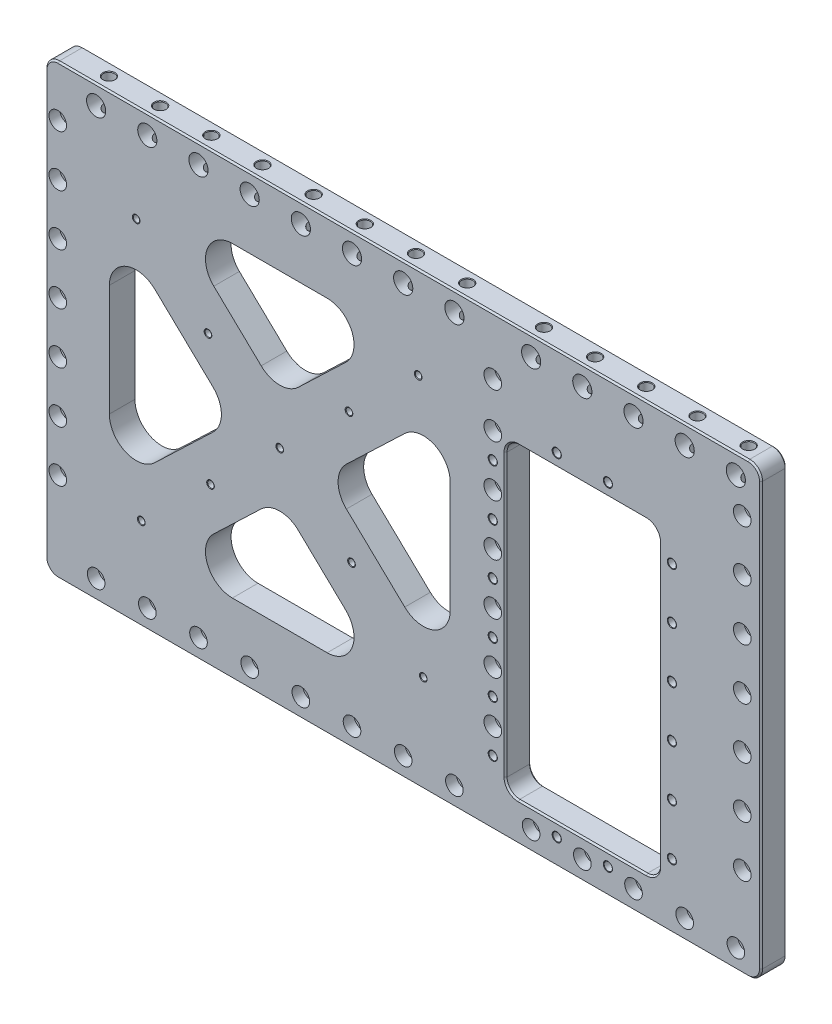
SolidWorks part; units mm, degrees
material "6061-T6 Al"
ref_plane "Front Plane" through (0, 0, 0) normal (0, 0, 1) x (1, 0, 0)
ref_plane "Top Plane" through (0, 0, 0) normal (0, 1, 0) x (1, 0, 0)
ref_plane "Right Plane" through (0, 0, 0) normal (1, 0, 0) x (0, 0, -1)
sketch "Sketch1" plane through (0, 0, 0) normal (0, 0, 1) x (1, 0, 0)
  line L0 (-355.219, -222.25) -> (355.219, 222.25) construction
  line L1 (-355.219, 222.25) -> (355.219, 222.25)
  line L2 (-355.219, 222.25) -> (-355.219, -222.25)
  line L3 (-355.219, -222.25) -> (355.219, -222.25)
  line L4 (355.219, 222.25) -> (355.219, -222.25)
  point P4 (0, 0)
  dimension "D1" = 710.438
  dimension "D2" = 444.5
extrude "Extrude1" add sketch "Sketch1" along normal mid plane 25.4
hole_wizard "CBORE for 3/8 Socket Head Cap Screw1" positions "Sketch3" profile "Sketch2" counterbore size "3/8" standard "Ansi Inch" end condition through all
sketch "Sketch3" plane through (0, 0, 12.7) normal (0, 0, 1) x (1, 0, 0)
  line L0 (-342.9, 19.05) -> (-355.219, 19.05) construction
  line L1 (-355.219, 222.25) -> (-355.219, -222.25) construction
  line L16 (-355.219, 222.25) -> (-355.219, -184.15) construction
  line L17 (336.55, 19.05) -> (-342.9, 19.05) construction
  point P0 (-342.9, 19.05)
  point P32 (336.55, 19.05)
  point P58 (-355.219, 19.05)
  dimension "D1" = 679.45
  dimension "D2" = 406.4
  dimension "D3" = 342.9
sketch "Sketch2" plane through (-342.9, 19.05, 12.7) normal (1, 0, 0) x (0, -1, 0)
  line L0 (0, 0) -> (0, 25.4)
  line L1 (5.1587, 24.614) -> (5.842, 25.4)
  line L2 (5.1587, 24.614) -> (5.1587, 10.668)
  line L3 (5.1587, 10.668) -> (8.7376, 10.668)
  line L4 (8.7376, 10.668) -> (8.7376, 0)
  line L5 (8.7376, 0) -> (0, 0)
  line L11 (0, -6.35) -> (0, 107.95) construction
  line L12 (5.842, 25.4) -> (0, 25.4)
  line L13 (-5.1587, 24.614) -> (-5.842, 25.4) construction
  dimension "Thru Hole Dia." = 10.3175
  dimension "Thru Hole Depth" = 25.4
  dimension "C'Bore Dia." = 17.4752
  dimension "C'Bore Depth" = 10.668
  dimension "Far C'Sink Dia." = 11.684
  dimension "Far C'Sink Angle" = 82
pattern_linear "LPattern1" count 4 spacing 50.8 along (0, -1, 0) count 4 spacing 50.8 along (0, 1, 0) of "CBORE for 3/8 Socket Head Cap Screw1"
sketch "Sketch9" plane through (0, 0, 12.7) normal (0, 0, 1) x (1, 0, 0)
  line L0 (-355.219, 222.25) -> (110.1219, -222.25) construction
  line L1 (-355.219, -222.25) -> (110.1219, 222.25) construction
  line L2 (-122.5485, 0) -> (-122.5485, 43.9073) construction
  line L3 (-122.5485, 0) -> (-168.5145, 0) construction
  line L4 (-8.9691, 152.4) -> (-122.5485, 43.9073)
  line L5 (-122.5485, 43.9073) -> (-236.128, 152.4)
  line L6 (-236.128, 152.4) -> (-8.9691, 152.4)
  line L7 (-291.719, 117.6866) -> (-168.5145, 0)
  line L8 (-168.5145, 0) -> (-291.719, -117.6866)
  line L9 (-291.719, -117.6866) -> (-291.719, 117.6866)
  line L10 (-122.5485, -43.9073) -> (-236.128, -152.4)
  line L11 (-236.128, -152.4) -> (-8.9691, -152.4)
  line L12 (-8.9691, -152.4) -> (-122.5485, -43.9073)
  line L13 (46.6219, 117.6866) -> (46.6219, -117.6866)
  line L14 (46.6219, -117.6866) -> (-76.5826, 0)
  line L15 (-76.5826, 0) -> (46.6219, 117.6866)
  line L16 (-122.5485, 0) -> (-76.5826, 0) construction
  line L17 (-122.5485, -43.9073) -> (-122.5485, 0) construction
  line L18 (355.219, 222.25) -> (-355.219, 222.25) construction
  line L20 (110.1219, -133.35) -> (110.1219, -222.25) construction
  line L21 (-355.219, 222.25) -> (-355.219, -222.25) construction
  dimension "D1" = 63.5
  dimension "D2" = 69.85
  dimension "D3" = 63.5
  dimension "D5" = 232.6705
extrude "Cut-Extrude2" cut sketch "Sketch9" against normal through all
fillet "Fillet2" radius 26.67 12 edges at (-236.128, 152.4, 0) (-8.9691, 152.4, 0) (-122.5485, 43.9073, 0) (-76.5826, 0, 0) (46.6219, 117.6866, 0) (46.6219, -117.6866, 0) (-8.9691, -152.4, 0) (-122.5485, -43.9073, 0) (-236.128, -152.4, 0) (-291.719, -117.6866, 0) (-168.5145, 0, 0) (-291.719, 117.6866, 0)
hole_wizard "CBORE for 3/8 Socket Head Cap Screw2" positions "Sketch5" profile "Sketch4" counterbore size "3/8" standard "Ansi Inch" end condition through all
sketch "Sketch5" plane through (0, 0, 12.7) normal (0, 0, 1) x (1, 0, 0)
  line L19 (355.219, 222.25) -> (-355.219, 222.25) construction
  point P74 (-152.4, -203.2)
  dimension "D1" = 425.45
  dimension "D2" = 152.4
sketch "Sketch4" plane through (-152.4, -203.2, 12.7) normal (1, 0, 0) x (0, -1, 0)
  line L0 (0, 0) -> (0, 25.4)
  line L1 (5.1587, 24.614) -> (5.842, 25.4)
  line L2 (5.1587, 24.614) -> (5.1587, 10.668)
  line L3 (5.1587, 10.668) -> (8.7376, 10.668)
  line L4 (8.7376, 10.668) -> (8.7376, 0)
  line L5 (8.7376, 0) -> (0, 0)
  line L11 (0, -6.35) -> (0, 107.95) construction
  line L12 (5.842, 25.4) -> (0, 25.4)
  line L13 (-5.1587, 24.614) -> (-5.842, 25.4) construction
  dimension "Thru Hole Dia." = 10.3175
  dimension "Thru Hole Depth" = 25.4
  dimension "C'Bore Dia." = 17.4752
  dimension "C'Bore Depth" = 10.668
  dimension "Far C'Sink Dia." = 11.684
  dimension "Far C'Sink Angle" = 82
hole_wizard "7/16 (0.4375) Diameter Hole1" positions "Sketch15" profile "Sketch14" hole size "7/16" standard "Ansi Inch"
sketch "Sketch15" plane through (0, 222.25, 0) normal (0, 1, 0) x (-1, 0, 0)
  line L10 (152.4, -12.7) -> (152.4, -11.914) construction
  point P0 (152.4, 0)
sketch "Sketch14" plane through (-152.4, 222.25, 0) normal (1, 0, 0) x (0, 0, 1)
  line L0 (0, 0) -> (0, 38.2635)
  line L1 (0, 38.2635) -> (5.5562, 34.925)
  line L2 (5.5562, 34.925) -> (5.5562, 0.6209)
  line L3 (5.5562, 0.6209) -> (6.096, 0)
  line L5 (6.096, 0) -> (0, 0)
  line L6 (-5.5562, 0.6209) -> (-6.096, 0) construction
  line L10 (0, 38.2635) -> (-5.5563, 34.925) construction
  line L11 (0, -6.35) -> (0, 107.95) construction
  dimension "Hole Dia." = 11.1125
  dimension "Hole Depth" = 34.925
  dimension "Near C'Sink Dia." = 12.192
  dimension "Near C'Sink Angle" = 82
  dimension "Drill Angle" = 118
hole_wizard "3/4 (0.75) Diameter Hole1" positions "Sketch13" profile "Sketch12" hole size "3/4" standard "Ansi Inch" end condition through all
sketch "Sketch13" plane through (0, 0, 12.7) normal (0, 0, 1) x (1, 0, 0)
  line L3 (-152.4, 187.325) -> (-152.4, 221.6291) construction
  line L4 (355.219, 222.25) -> (-355.219, 222.25) construction
  point P0 (-152.4, 203.2)
  dimension "D1" = 19.05
sketch "Sketch12" plane through (-152.4, 203.2, 12.7) normal (1, 0, 0) x (0, -1, 0)
  line L0 (0, 0) -> (0, 25.4)
  line L1 (0, 25.4) -> (9.525, 25.4)
  line L2 (9.525, 25.4) -> (9.525, 0)
  line L5 (9.525, 0) -> (0, 0)
  line L11 (0, -6.35) -> (0, 107.95) construction
  dimension "Thru Hole Dia." = 19.05
  dimension "Thru Hole Depth" = 25.4
pattern_linear "LPattern4" count 4 spacing 50.8 along (-1, 0, 0) count 5 spacing 50.8 along (1, 0, 0) of "7/16 (0.4375) Diameter Hole1", "3/4 (0.75) Diameter Hole1", "CBORE for 3/8 Socket Head Cap Screw2"
hole_wizard "CBORE for 3/8 Socket Head Cap Screw3" positions "Sketch17" profile "Sketch16" counterbore size "3/8" standard "Ansi Inch" end condition through all
sketch "Sketch17" plane through (0, 0, 12.7) normal (0, 0, 1) x (1, 0, 0)
  line L1 (88.9, 19.05) -> (336.55, 19.05) construction
  circle A2 centre (336.55, 19.05) radius 5.1587 construction
  point P67 (88.9, 19.05)
  dimension "D2" = 247.65
sketch "Sketch16" plane through (88.9, 19.05, 12.7) normal (1, 0, 0) x (0, -1, 0)
  line L0 (0, 0) -> (0, 25.4)
  line L1 (5.1587, 24.614) -> (5.842, 25.4)
  line L2 (5.1587, 24.614) -> (5.1587, 10.668)
  line L3 (5.1587, 10.668) -> (8.7376, 10.668)
  line L4 (8.7376, 10.668) -> (8.7376, 0)
  line L5 (8.7376, 0) -> (0, 0)
  line L11 (0, -6.35) -> (0, 107.95) construction
  line L12 (5.842, 25.4) -> (0, 25.4)
  line L13 (-5.1587, 24.614) -> (-5.842, 25.4) construction
  dimension "Thru Hole Dia." = 10.3175
  dimension "Thru Hole Depth" = 25.4
  dimension "C'Bore Dia." = 17.4752
  dimension "C'Bore Depth" = 10.668
  dimension "Far C'Sink Dia." = 11.684
  dimension "Far C'Sink Angle" = 82
pattern_linear "LPattern5" count 3 spacing 50.8 along (0, 1, 0) count 4 spacing 50.8 along (0, -1, 0) of "CBORE for 3/8 Socket Head Cap Screw3"
hole_wizard "CBORE for 3/8 Socket Head Cap Screw4" positions "Sketch26" profile "Sketch27" counterbore size "3/8" standard "Ansi Inch" end condition through all
sketch "Sketch26" plane through (0, 0, 12.7) normal (0, 0, 1) x (1, 0, 0)
  line L0 (88.9, 165.1) -> (88.9, 120.65) construction
  point P67 (88.9, 165.1)
  dimension "D1" = 44.45
sketch "Sketch27" plane through (88.9, 165.1, 12.7) normal (1, 0, 0) x (0, -1, 0)
  line L0 (0, 0) -> (0, 25.4)
  line L1 (5.1587, 24.614) -> (5.842, 25.4)
  line L2 (5.1587, 24.614) -> (5.1587, 10.668)
  line L3 (5.1587, 10.668) -> (8.7376, 10.668)
  line L4 (8.7376, 10.668) -> (8.7376, 0)
  line L5 (8.7376, 0) -> (0, 0)
  line L11 (0, -6.35) -> (0, 107.95) construction
  line L12 (5.842, 25.4) -> (0, 25.4)
  line L13 (-5.1587, 24.614) -> (-5.842, 25.4) construction
  dimension "Thru Hole Dia." = 10.3175
  dimension "Thru Hole Depth" = 25.4
  dimension "C'Bore Dia." = 17.4752
  dimension "C'Bore Depth" = 10.668
  dimension "Far C'Sink Dia." = 11.684
  dimension "Far C'Sink Angle" = 82
hole_wizard "1/4-20 Tapped Hole1" positions "Sketch25" profile "Sketch24" tap size "1/4-20" standard "Ansi Inch" end condition through all
sketch "Sketch25" plane through (0, 0, 12.7) normal (0, 0, 1) x (1, 0, 0)
  line L1 (-64.6412, 0) -> (-180.4559, 0) construction
  line L7 (-75.5009, -125.73) -> (19.9519, -125.73) construction
  line L8 (19.9519, -125.73) -> (19.9519, -55.3289) construction
  line L11 (19.9519, -125.73) -> (-122.5485, 0) construction
  line L12 (-122.5485, 0) -> (14.8706, 131.2646) construction
  line L15 (-122.5485, 0) -> (-265.049, 125.73) construction
  line L18 (-122.5485, 0) -> (-259.9677, -131.2646) construction
  line L21 (-140.9703, -61.504) -> (-188.0179, -106.4445) construction
  arc A0 (-56.3929, 19.2855) -> (-56.3929, -19.2855) centre (-37.9712, 0) ccw construction
  arc A1 (-188.7042, -19.2855) -> (-188.7042, 19.2855) centre (-207.1259, 0) ccw construction
  point P0 (19.9519, -125.73)
  point P1 (-122.5485, 0)
  point P3 (-51.2983, -62.865)
  point P5 (-53.839, 65.6323)
  point P7 (14.8706, 131.2646)
  point P9 (-265.049, 125.73)
  point P11 (-193.7988, 62.865)
  point P13 (-191.2581, -65.6323)
  point P15 (-259.9677, -131.2646)
sketch "Sketch24" plane through (19.9519, -125.73, 12.7) normal (1, 0, 0) x (0, -1, 0)
  line L0 (0, 0) -> (0, 25.4)
  line L1 (0, 25.4) -> (2.5527, 25.4)
  line L3 (2.5527, 25.4) -> (2.5527, 12.7)
  line L4 (3.175, 12.7) -> (2.5527, 12.7)
  line L5 (3.175, 12.7) -> (3.175, 0.3666)
  line L6 (3.175, 0.3666) -> (3.81, 0)
  line L7 (3.81, 0) -> (0, 0)
  line L8 (-3.175, 0.3666) -> (-3.81, 0) construction
  line L11 (0, -6.35) -> (0, 107.95) construction
  dimension "Thru Tap Drill Dia." = 5.1054
  dimension "Thru Tap Drill Depth" = 25.4
  dimension "Thread Major Dia." = 6.35
  dimension "Thread Depth" = 12.7
  dimension "Near C'Sink Dia." = 7.62
  dimension "Near C'Sink Angle" = 120
hole_wizard "CBORE for 3/8 Socket Head Cap Screw5" positions "Sketch29" profile "Sketch30" counterbore size "3/8" standard "Ansi Inch" end condition through all
sketch "Sketch29" plane through (0, 0, 12.7) normal (0, 0, 1) x (1, 0, 0)
  line L0 (127, -203.2) -> (50.8, -203.2) construction
  circle A0 centre (88.9, -133.35) radius 5.842 construction
  point P74 (127, -203.2)
  dimension "D1" = 38.1
sketch "Sketch30" plane through (127, -203.2, 12.7) normal (1, 0, 0) x (0, -1, 0)
  line L0 (0, 0) -> (0, 25.4)
  line L1 (5.1587, 24.614) -> (5.842, 25.4)
  line L2 (5.1587, 24.614) -> (5.1587, 10.668)
  line L3 (5.1587, 10.668) -> (8.7376, 10.668)
  line L4 (8.7376, 10.668) -> (8.7376, 0)
  line L5 (8.7376, 0) -> (0, 0)
  line L11 (0, -6.35) -> (0, 107.95) construction
  line L12 (5.842, 25.4) -> (0, 25.4)
  line L13 (-5.1587, 24.614) -> (-5.842, 25.4) construction
  dimension "Thru Hole Dia." = 10.3175
  dimension "Thru Hole Depth" = 25.4
  dimension "C'Bore Dia." = 17.4752
  dimension "C'Bore Depth" = 10.668
  dimension "Far C'Sink Dia." = 11.684
  dimension "Far C'Sink Angle" = 82
hole_wizard "7/16 (0.4375) Diameter Hole2" positions "Sketch31" profile "Sketch32" hole size "7/16" standard "Ansi Inch"
sketch "Sketch31" plane through (0, 222.25, 0) normal (0, 1, 0) x (-1, 0, 0)
  line L11 (-127, -12.7) -> (-127, -11.914) construction
  point P0 (-127, 0)
sketch "Sketch32" plane through (127, 222.25, 0) normal (1, 0, 0) x (0, 0, 1)
  line L0 (0, 0) -> (0, 38.2635)
  line L1 (0, 38.2635) -> (5.5562, 34.925)
  line L2 (5.5562, 34.925) -> (5.5562, 0.6209)
  line L3 (5.5562, 0.6209) -> (6.096, 0)
  line L5 (6.096, 0) -> (0, 0)
  line L6 (-5.5562, 0.6209) -> (-6.096, 0) construction
  line L10 (0, 38.2635) -> (-5.5563, 34.925) construction
  line L11 (0, -6.35) -> (0, 107.95) construction
  dimension "Hole Dia." = 11.1125
  dimension "Hole Depth" = 34.925
  dimension "Near C'Sink Dia." = 12.192
  dimension "Near C'Sink Angle" = 82
  dimension "Drill Angle" = 118
hole_wizard "3/4 (0.75) Diameter Hole2" positions "Sketch33" profile "Sketch34" hole size "3/4" standard "Ansi Inch" end condition through all
sketch "Sketch33" plane through (0, 0, 12.7) normal (0, 0, 1) x (1, 0, 0)
  line L5 (127, 187.325) -> (127, 221.6291) construction
  point P0 (127, 203.2)
sketch "Sketch34" plane through (127, 203.2, 12.7) normal (1, 0, 0) x (0, -1, 0)
  line L0 (0, 0) -> (0, 25.4)
  line L1 (0, 25.4) -> (9.525, 25.4)
  line L2 (9.525, 25.4) -> (9.525, 0)
  line L5 (9.525, 0) -> (0, 0)
  line L11 (0, -6.35) -> (0, 107.95) construction
  dimension "Thru Hole Dia." = 19.05
  dimension "Thru Hole Depth" = 25.4
pattern_linear "LPattern6" count 5 spacing 50.8 along (1, 0, 0) of "CBORE for 3/8 Socket Head Cap Screw5", "7/16 (0.4375) Diameter Hole2", "3/4 (0.75) Diameter Hole2"
fillet "Fillet3" radius 12.7 4 edges at (355.219, -222.25, 0) (-355.219, -222.25, 0) (355.219, 222.25, 0) (-355.219, 222.25, 0)
chamfer "Chamfer1" distance 1.524 angle 45 16 edges at (355.219, 0, -12.7) (351.4993, 218.5303, -12.7) (351.4993, -218.5303, -12.7) (0, 222.25, -12.7) (0, -222.25, -12.7) (-351.4993, 218.5303, -12.7) (-351.4993, -218.5303, -12.7) (-355.219, 0, -12.7) (355.219, 0, 12.7) (351.4993, 218.5303, 12.7) (351.4993, -218.5303, 12.7) (0, 222.25, 12.7) (0, -222.25, 12.7) (-351.4993, 218.5303, 12.7) (-351.4993, -218.5303, 12.7) (-355.219, 0, 12.7)
sketch "Sketch35" plane through (0, 0, 12.7) normal (0, 0, 1) x (1, 0, 0)
  line L1 (114.3, 120.65) -> (241.3, 120.65)
  line L2 (101.6, 107.95) -> (101.6, -171.45)
  line L3 (114.3, -184.15) -> (241.3, -184.15)
  line L4 (254, 107.95) -> (254, -171.45)
  line L12 (342.519, -222.25) -> (-342.519, -222.25) construction
  line L14 (127, -203.2) -> (101.6, -203.2) construction
  line L15 (228.6, -203.2) -> (254, -203.2) construction
  arc A0 (114.3, 120.65) -> (101.6, 107.95) centre (114.3, 107.95) ccw
  arc A1 (241.3, 120.65) -> (254, 107.95) centre (241.3, 107.95) cw
  arc A2 (254, -171.45) -> (241.3, -184.15) centre (241.3, -171.45) cw
  arc A3 (101.6, -171.45) -> (114.3, -184.15) centre (114.3, -171.45) ccw
  circle A4 centre (88.9, 69.85) radius 5.1587 construction
  dimension "D1" = 12.7
  dimension "D3" = 12.7
  dimension "D2" = 330.2
  dimension "D4" = 38.1
extrude "Cut-Extrude5" cut sketch "Sketch35" against normal through all
hole_wizard "Tapped Hole for 1/4-20 Helicoil1" positions "Sketch37" profile "Sketch36" tap size "1/4-20" standard "Helicoil® Inch" end condition through all
sketch "Sketch37" plane through (0, 0, 12.7) normal (0, 0, 1) x (1, 0, 0)
  line L64 (152.4, -196.85) -> (203.2, -196.85) construction
  line L69 (152.4, 133.35) -> (203.2, 133.35) construction
  line L91 (88.9, 95.25) -> (88.9, 69.85) construction
  line L92 (88.9, 69.85) -> (88.9, 44.45) construction
  line L93 (88.9, 44.45) -> (88.9, -6.35) construction
  line L94 (88.9, -6.35) -> (88.9, -57.15) construction
  line L95 (88.9, -57.15) -> (88.9, -107.95) construction
  line L96 (88.9, -107.95) -> (88.9, -158.75) construction
  line L99 (266.7, 95.25) -> (266.7, 44.45) construction
  line L100 (266.7, 44.45) -> (266.7, -6.35) construction
  line L101 (266.7, -6.35) -> (266.7, -57.15) construction
  line L102 (266.7, -57.15) -> (266.7, -107.95) construction
  line L103 (266.7, -107.95) -> (266.7, -158.75) construction
  line L104 (88.9, 120.65) -> (88.9, 95.25) construction
  line L113 (177.8, 120.65) -> (177.8, 133.35) construction
  line L114 (241.3, 120.65) -> (114.3, 120.65) construction
  line L117 (177.8, -196.85) -> (177.8, -184.15) construction
  line L118 (114.3, -184.15) -> (241.3, -184.15) construction
  point P3 (88.9, -6.35)
  point P5 (88.9, -57.15)
  point P7 (88.9, -107.95)
  point P9 (88.9, -158.75)
  point P11 (152.4, -196.85)
  point P13 (203.2, -196.85)
  point P15 (266.7, -158.75)
  point P17 (266.7, -107.95)
  point P19 (266.7, -57.15)
  point P21 (266.7, -6.35)
  point P23 (266.7, 44.45)
  point P25 (266.7, 95.25)
  point P27 (152.4, 133.35)
  point P29 (203.2, 133.35)
  point P221 (88.9, 44.45)
  point P223 (88.9, 95.25)
  dimension "D1" = 330.2
  dimension "D2" = 177.8
sketch "Sketch36" plane through (88.9, -6.35, 12.7) normal (1, 0, 0) x (0, -1, 0)
  line L0 (0, 0) -> (0, 25.4)
  line L1 (3.3782, 24.9033) -> (3.81, 25.4)
  line L2 (4.0475, 15.7226) -> (3.3782, 15.7226)
  line L3 (3.3782, 15.7226) -> (3.3782, 24.9033)
  line L5 (4.0475, 15.7226) -> (4.0475, 0.3028)
  line L6 (4.0475, 0.3028) -> (4.572, 0)
  line L7 (4.572, 0) -> (0, 0)
  line L8 (-4.0475, 0.3028) -> (-4.572, 0) construction
  line L11 (0, -6.35) -> (0, 107.95) construction
  line L12 (3.81, 25.4) -> (0, 25.4)
  line L13 (-3.3782, 24.9033) -> (-3.81, 25.4) construction
  dimension "Thru Tap Drill Dia." = 6.7564
  dimension "Thru Tap Drill Depth" = 25.4
  dimension "Thread Major Dia." = 8.095
  dimension "Thread Depth" = 15.7226
  dimension "Near C'Sink Dia." = 9.144
  dimension "Near C'Sink Angle" = 120
  dimension "Far C'Sink Dia." = 7.62
  dimension "Far C'Sink Angle" = 82
chamfer "Chamfer2" distance 1.524 angle 45 16 edges at (177.8, 120.65, -12.7) (105.3197, 116.9303, -12.7) (250.2803, 116.9303, -12.7) (101.6, -31.75, -12.7) (254, -31.75, -12.7) (105.3197, -180.4303, -12.7) (250.2803, -180.4303, -12.7) (177.8, -184.15, -12.7) (177.8, 120.65, 12.7) (105.3197, 116.9303, 12.7) (250.2803, 116.9303, 12.7) (101.6, -31.75, 12.7) (254, -31.75, 12.7) (105.3197, -180.4303, 12.7) (250.2803, -180.4303, 12.7) (177.8, -184.15, 12.7)
sketch "Sketch38" plane through (101.6, 0, 0) normal (1, 0, 0) x (0, 0, -1)
  line L0 (12.7, 97.7387) -> (12.7, 92.7613)
  line L1 (12.7, 209.55) -> (12.7, -209.55) construction
  line L2 (1.7525, 99.2975) -> (1.7525, 91.2025) construction
  line L3 (3.0226, 99.2975) -> (-12.3972, 99.2975) construction
  line L4 (-12.3972, 91.2025) -> (3.0226, 91.2025) construction
  arc A0 (12.7, 97.7387) -> (12.7, 92.7613) centre (18.542, 95.25) ccw
  point P11 (1.7525, 95.25)
  dimension "D1" = 6.35
  dimension "D2" = 0.508
extrude "Extrude2" cut sketch "Sketch38" against normal blind 12.7
pattern_linear "LPattern7" count 6 spacing 50.8 along (0, -1, 0) of "Extrude2"
sketch "Sketch39" plane through (0, -184.15, 0) normal (0, 1, 0) x (1, 0, 0)
  line L0 (149.9113, 12.7) -> (154.8887, 12.7)
  line L1 (148.3525, -0.9111) -> (156.4475, -0.9111) construction
  line L2 (148.3525, 3.0226) -> (148.3525, -12.3972) construction
  line L3 (156.4475, -12.3972) -> (156.4475, 3.0226) construction
  line L4 (-342.519, 12.7) -> (342.519, 12.7) construction
  arc A0 (149.9113, 12.7) -> (154.8887, 12.7) centre (152.4, 18.542) ccw
  point P9 (152.4, -0.9111)
  dimension "D1" = 6.35
  dimension "D2" = 0.508
extrude "Extrude3" cut sketch "Sketch39" against normal blind 12.7
pattern_linear "LPattern8" count 2 spacing 50.8 along (1, 0, 0) of "Extrude3"
